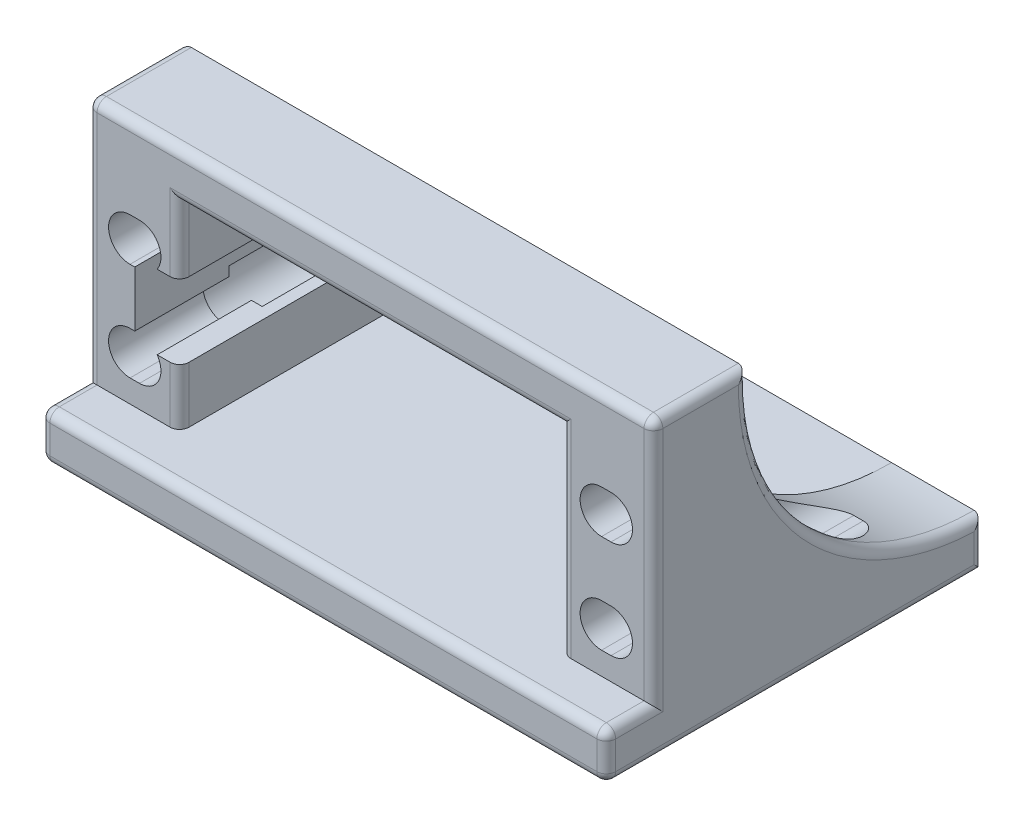
SolidWorks part; units mm, degrees
material "ABS"
ref_plane "Front Plane" through (0, 0, 0) normal (0, 0, 1) x (1, 0, 0)
ref_plane "Top Plane" through (0, 0, 0) normal (0, 1, 0) x (1, 0, 0)
ref_plane "Right Plane" through (0, 0, 0) normal (1, 0, 0) x (0, 0, -1)
sketch "Sketch1" plane through (0, 0, 0) normal (0, 1, 0) x (1, 0, 0)
  line L1 (0, 0) -> (60, 0)
  line L2 (0, 0) -> (0, 40)
  line L3 (0, 40) -> (60, 40)
  line L4 (60, 0) -> (60, 40)
  dimension "D1" = 60
  dimension "D2" = 40
extrude "Boss-Extrude1" add sketch "Sketch1" along normal blind 5
sketch "Sketch2" plane through (0, 5, 0) normal (0, 1, 0) x (1, 0, 0)
  line L0 (0, 40) -> (0, 0) construction
  line L1 (0, 5) -> (9.75, 5)
  line L2 (0, 5) -> (0, 15)
  line L3 (0, 15) -> (9.75, 15)
  line L4 (9.75, 5) -> (9.75, 15)
  line L5 (60, 0) -> (60, 40) construction
  line L6 (60, 5) -> (50.25, 5)
  line L7 (60, 5) -> (60, 15)
  line L8 (60, 15) -> (50.25, 15)
  line L9 (50.25, 5) -> (50.25, 15)
  line L10 (0, 0) -> (60, 0) construction
  dimension "D1" = 10
  dimension "D2" = 40.5
  dimension "D3" = 5
extrude "Boss-Extrude2" add sketch "Sketch2" along normal blind 26
sketch "Sketch3" plane through (0, 0, 0) normal (-1, 0, 0) x (0, 0, 1)
  line L0 (-15, 30) -> (-15, 5)
  line L1 (-15, 5) -> (-40, 5)
  line L4 (-15, 31) -> (-15, 5) construction
  arc A0 (-40, 5) -> (-15, 30) centre (-40, 30) ccw
  dimension "D1" = 25
extrude "Boss-Extrude3" add sketch "Sketch3" against normal blind 9.75
ref_plane "Plane4" through (30, 0, 0) normal (1, 0, 0) x (0, 0, -1)
mirror "Mirror2" about plane through (30, 0, 0) normal (1, 0, 0) of "Boss-Extrude3"
sketch "Sketch4" plane through (0, 0, -5) normal (0, 0, 1) x (1, 0, 0)
  line L0 (0, 20.113) -> (60, 20.113) construction
  line L1 (0, 31) -> (0, 5) construction
  line L2 (60, 31) -> (60, 5) construction
  line L3 (0, 5) -> (60, 5) construction
  line L4 (0, 9.677) -> (60, 9.677) construction
  line L5 (0, 5) -> (9.75, 5) construction
  line L6 (4.5, 20.113) -> (5.5, 20.113) construction
  line L7 (4.5, 22.388) -> (5.5, 22.388)
  line L8 (4.5, 17.838) -> (5.5, 17.838)
  line L9 (4.5, 9.677) -> (5.5, 9.677) construction
  line L10 (4.5, 11.952) -> (5.5, 11.952)
  line L11 (4.5, 7.402) -> (5.5, 7.402)
  line L12 (30, 0) -> (30, 31) construction
  line L13 (0, 0) -> (60, 0) construction
  line L16 (55.5, 9.677) -> (54.5, 9.677) construction
  line L17 (55.5, 11.952) -> (54.5, 11.952)
  line L18 (55.5, 7.402) -> (54.5, 7.402)
  line L19 (55.5, 20.113) -> (54.5, 20.113) construction
  line L20 (55.5, 22.388) -> (54.5, 22.388)
  line L21 (55.5, 17.838) -> (54.5, 17.838)
  arc A0 (4.5, 22.388) -> (4.5, 17.838) centre (4.5, 20.113) ccw
  arc A1 (5.5, 17.838) -> (5.5, 22.388) centre (5.5, 20.113) ccw
  arc A2 (4.5, 11.952) -> (4.5, 7.402) centre (4.5, 9.677) ccw
  arc A3 (5.5, 7.402) -> (5.5, 11.952) centre (5.5, 9.677) ccw
  arc A4 (55.5, 11.952) -> (55.5, 7.402) centre (55.5, 9.677) cw
  arc A5 (54.5, 7.402) -> (54.5, 11.952) centre (54.5, 9.677) cw
  arc A6 (55.5, 22.388) -> (55.5, 17.838) centre (55.5, 20.113) cw
  arc A7 (54.5, 17.838) -> (54.5, 22.388) centre (54.5, 20.113) cw
  point P14 (5, 20.113)
  point P19 (5, 9.677)
  point P36 (55, 9.677)
  point P43 (55, 20.113)
  dimension "D3" = 2.275
  dimension "D1" = 15.113
  dimension "D2" = 4.677
  dimension "D4" = 1
  dimension "D5" = 5
extrude "Cut-Extrude1" cut sketch "Sketch4" against normal through all
sketch "Sketch5" plane through (9.75, 0, 0) normal (1, 0, 0) x (0, 0, -1)
  line L0 (5, 31) -> (5, 5) construction
  line L1 (15, 31) -> (5, 31)
  line L2 (15, 31) -> (15, 26)
  line L3 (15, 26) -> (5, 26)
  line L4 (5, 31) -> (5, 26)
  dimension "D1" = 5
extrude "Boss-Extrude4" add sketch "Sketch5" along normal up to surface (40.5 mm away) up to face at (50.25, 19.3645, -14.9645)
sketch "Sketch6" plane through (0, 0, -5) normal (0, 0, 1) x (1, 0, 0)
  line L2 (4.5, 17.838) -> (5.5, 17.838) construction
  line L3 (5.5, 22.388) -> (4.5, 22.388) construction
  line L4 (4.5, 17.838) -> (5.5, 17.838)
  line L5 (5.5, 22.388) -> (4.5, 22.388)
  line L6 (4.5, 7.402) -> (5.5, 7.402) construction
  line L7 (5.5, 11.952) -> (4.5, 11.952) construction
  line L8 (4.5, 7.402) -> (5.5, 7.402)
  line L9 (5.5, 11.952) -> (4.5, 11.952)
  line L10 (9.75, 26) -> (9.75, 5) construction
  line L11 (9.75, 18.8246) -> (5, 18.8246)
  line L12 (9.75, 18.8246) -> (9.75, 10.9654)
  line L13 (9.75, 10.9654) -> (5, 10.9654)
  line L14 (5, 18.8246) -> (5, 10.9654)
  arc A3 (4.5, 22.388) -> (4.5, 17.838) centre (4.5, 20.113) ccw construction
  arc A4 (5.5, 17.838) -> (5.5, 22.388) centre (5.5, 20.113) ccw construction
  arc A5 (4.5, 22.388) -> (4.5, 17.838) centre (4.5, 20.113) ccw
  arc A6 (5.5, 17.838) -> (5.5, 22.388) centre (5.5, 20.113) ccw
  arc A7 (4.5, 11.952) -> (4.5, 7.402) centre (4.5, 9.677) ccw construction
  arc A8 (5.5, 7.402) -> (5.5, 11.952) centre (5.5, 9.677) ccw construction
  arc A9 (4.5, 11.952) -> (4.5, 7.402) centre (4.5, 9.677) ccw
  arc A10 (5.5, 7.402) -> (5.5, 11.952) centre (5.5, 9.677) ccw
  point P18 (7.375, 18.8246)
  point P19 (7.375, 10.9654)
  point P20 (5, 11.952)
  arc M16 (5.5, 11.952) -> (5.5, 7.402) centre (5.5, 9.677) cw
  line M17 (5.5, 17.838) -> (4.5, 17.838)
  arc M20 (5.5, 22.388) -> (5.5, 17.838) centre (5.5, 20.113) cw
  line M22 (9.75, 5) -> (9.75, 26)
extrude "Wire_Cut_Out" cut sketch "Sketch6" against normal through all contours L14 L9 L13 L11 M17 M16 M22 M20 | L11 L14 M17 M20 | L9 L14 L13 M16
sketch "Sketch8" plane through (0, 0, -40) normal (0, 0, -1) x (-1, 0, 0)
  line L0 (-54.5, 7.402) -> (-55.5, 7.402) construction
  line L1 (-55.5, 11.952) -> (-54.5, 11.952) construction
  line L2 (-55.5, 22.388) -> (-54.5, 22.388) construction
  line L3 (-54.5, 17.838) -> (-55.5, 17.838) construction
  line L4 (-54.5, 7.402) -> (-55.5, 7.402)
  line L5 (-55.5, 11.952) -> (-54.5, 11.952)
  line L6 (-55.5, 22.388) -> (-54.5, 22.388)
  line L7 (-54.5, 17.838) -> (-55.5, 17.838)
  line L8 (-4.5, 22.388) -> (-5.5, 22.388) construction
  line L9 (-4.5, 22.388) -> (-5.5, 22.388)
  line L10 (-5.5, 7.402) -> (-4.5, 7.402) construction
  line L11 (-5.5, 7.402) -> (-4.5, 7.402)
  line L12 (-55.5, 20.113) -> (-54.5, 20.113) construction
  line L13 (-55.5, 23.388) -> (-54.5, 23.388)
  line L14 (-55.5, 16.838) -> (-54.5, 16.838)
  line L15 (-55.5, 9.677) -> (-54.5, 9.677) construction
  line L16 (-55.5, 12.952) -> (-54.5, 12.952)
  line L17 (-55.5, 6.402) -> (-54.5, 6.402)
  line L18 (-5.5, 20.113) -> (-4.5, 20.113) construction
  line L19 (-5.5, 23.388) -> (-4.5, 23.388)
  line L20 (-5.5, 16.838) -> (-4.5, 16.838)
  line L21 (-5.5, 9.677) -> (-4.5, 9.677) construction
  line L22 (-5.5, 12.952) -> (-4.5, 12.952)
  line L23 (-5.5, 6.402) -> (-4.5, 6.402)
  arc A0 (-55.5, 11.952) -> (-55.5, 7.402) centre (-55.5, 9.677) ccw construction
  arc A1 (-54.5, 7.402) -> (-54.5, 11.952) centre (-54.5, 9.677) ccw construction
  arc A2 (-55.5, 22.388) -> (-55.5, 17.838) centre (-55.5, 20.113) ccw construction
  arc A3 (-54.5, 17.838) -> (-54.5, 22.388) centre (-54.5, 20.113) ccw construction
  arc A4 (-55.5, 11.952) -> (-55.5, 7.402) centre (-55.5, 9.677) ccw
  arc A5 (-54.5, 7.402) -> (-54.5, 11.952) centre (-54.5, 9.677) ccw
  arc A6 (-55.5, 22.388) -> (-55.5, 17.838) centre (-55.5, 20.113) ccw
  arc A7 (-54.5, 17.838) -> (-54.5, 22.388) centre (-54.5, 20.113) ccw
  arc A8 (-4.5, 17.838) -> (-4.5, 22.388) centre (-4.5, 20.113) ccw construction
  arc A9 (-5.5, 22.388) -> (-7.375, 18.8246) centre (-5.5, 20.113) ccw construction
  arc A10 (-4.5, 17.838) -> (-4.5, 22.388) centre (-4.5, 20.113) ccw
  arc A11 (-5.5, 22.388) -> (-7.375, 18.8246) centre (-5.5, 20.113) ccw
  arc A12 (-7.375, 10.9654) -> (-5.5, 7.402) centre (-5.5, 9.677) ccw construction
  arc A13 (-4.5, 7.402) -> (-4.5, 11.952) centre (-4.5, 9.677) ccw construction
  arc A14 (-7.375, 10.9654) -> (-5.5, 7.402) centre (-5.5, 9.677) ccw
  arc A15 (-4.5, 7.402) -> (-4.5, 11.952) centre (-4.5, 9.677) ccw
  arc A16 (-55.5, 23.388) -> (-55.5, 16.838) centre (-55.5, 20.113) ccw
  arc A17 (-54.5, 16.838) -> (-54.5, 23.388) centre (-54.5, 20.113) ccw
  arc A18 (-55.5, 12.952) -> (-55.5, 6.402) centre (-55.5, 9.677) ccw
  arc A19 (-54.5, 6.402) -> (-54.5, 12.952) centre (-54.5, 9.677) ccw
  arc A20 (-5.5, 23.388) -> (-5.5, 16.838) centre (-5.5, 20.113) ccw
  arc A21 (-4.5, 16.838) -> (-4.5, 23.388) centre (-4.5, 20.113) ccw
  arc A22 (-5.5, 12.952) -> (-5.5, 6.402) centre (-5.5, 9.677) ccw
  arc A23 (-4.5, 6.402) -> (-4.5, 12.952) centre (-4.5, 9.677) ccw
  point P21 (-55, 20.113)
  point P29 (-55, 9.677)
  point P34 (-5, 20.113)
  point P39 (-5, 9.677)
  dimension "D1" = 1
extrude "Washer_Cut_Out" cut sketch "Sketch8" against normal blind 25
fillet "Fillet1" radius 1 25 edges at (60, 0, -20) (60, 5, -2.5) (60, 18, -5) (60, 31, -10) (60, 30.5, -15) (60, 12.3223, -22.3223) (60, 2.5, -40) (30, 5, 0) (60, 2.5, 0) (30, 0, 0) (0, 2.5, -40) (0, 12.3223, -22.3223) (0, 30.5, -15) (0, 31, -10) (0, 18, -5) (0, 5, -2.5) (0, 2.5, 0) (0, 0, -20) (9.75, 7.9827, -5) (9.75, 22.4123, -5) (50.25, 15.5, -5) (30, 26, -15) (30, 26, -5) (9.75, 6.5387, -31.3647) (30, 31, -5)
